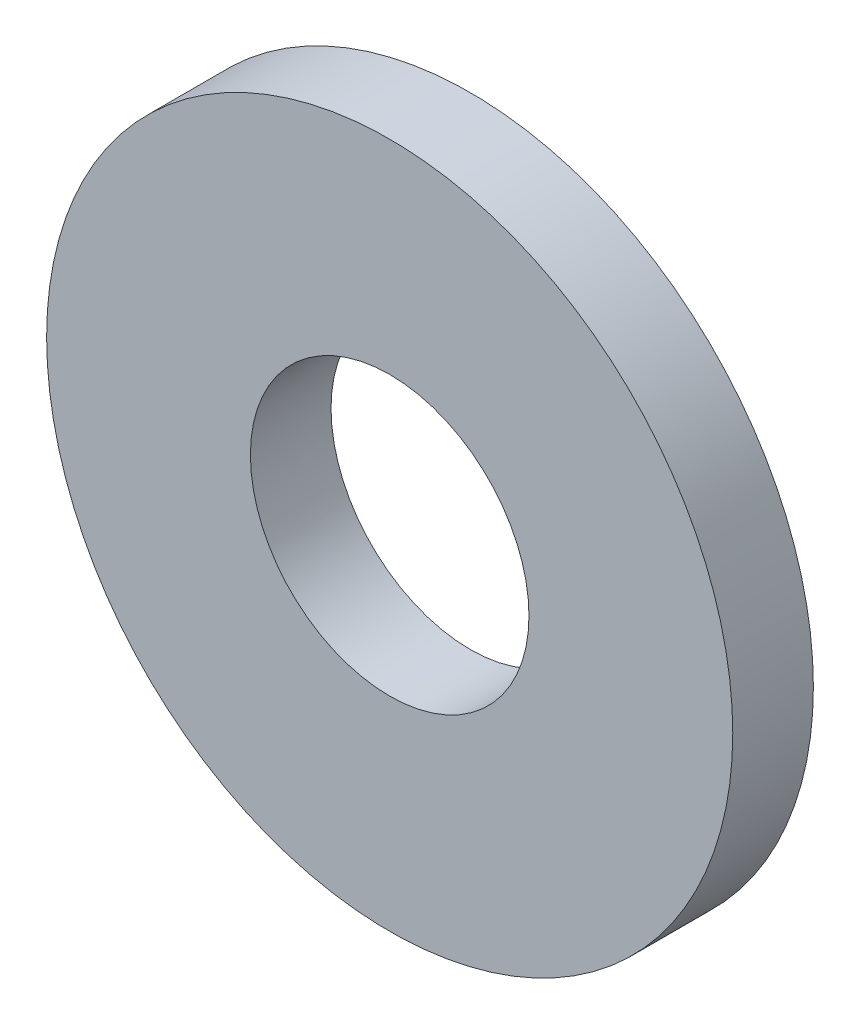
SolidWorks part; units mm, degrees
ref_plane "Front Plane" through (0, 0, 0) normal (0, 0, 1) x (1, 0, 0)
ref_plane "Top Plane" through (0, 0, 0) normal (0, 1, 0) x (1, 0, 0)
ref_plane "Right Plane" through (0, 0, 0) normal (1, 0, 0) x (0, 0, -1)
sketch "Sketch1" plane through (0, 0, 0) normal (1, 0, 0) x (0, 0, -1)
  line L0 (0, -5.1562) -> (0, 5.1562) construction
  line L1 (0, -12.7) -> (0, 12.7) construction
  line L2 (-1.4923, 12.7) -> (1.4922, 12.7)
  point P4 (0, 0)
  point P8 (0, 0)
  point P10 (0, 12.7)
  dimension "Thickness" = 2.9845
sketch "Sketch2" plane through (0, 0, 0) normal (0, 0, 1) x (1, 0, 0)
  line L1 (0, -5.1562) -> (0, 5.1562) construction
  circle A2 centre (0, 0) radius 5.1562
  circle A3 centre (0, 0) radius 12.7
  point P3 (0, 0)
  dimension "D1" = 10.3124
  dimension "D2" = 25.4
extrude "Boss-Extrude1" add sketch "Sketch2" along normal mid plane 2.9845
equation "\"D1@Boss-Extrude1\"=\"Thickness@Sketch1\""
equation "\"D1@Sketch2\"=\"ID@Sketch1\""
equation "\"D2@Sketch2\"=\"OD@Sketch1\""
